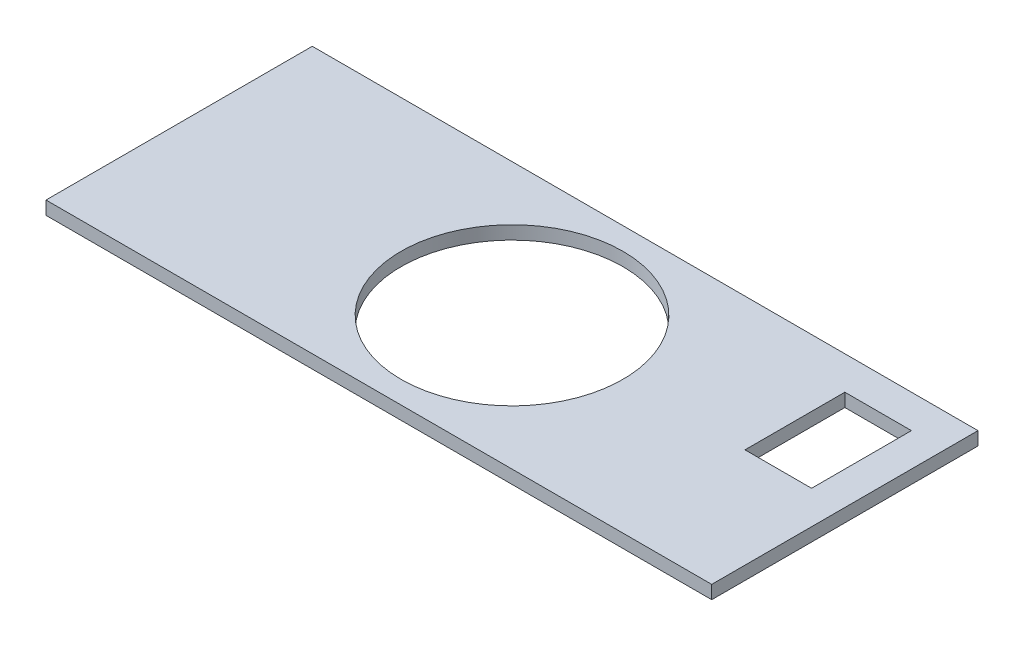
SolidWorks part; units mm, degrees
ref_plane "Front Plane" through (0, 0, 0) normal (0, 0, 1) x (1, 0, 0)
ref_plane "Top Plane" through (0, 0, 0) normal (0, 1, 0) x (1, 0, 0)
ref_plane "Right Plane" through (0, 0, 0) normal (1, 0, 0) x (0, 0, -1)
sketch "Sketch1" plane through (0, 0, 0) normal (0, 1, 0) x (1, 0, 0)
  line L0 (150, 120) -> (150, 60)
  line L1 (0, 0) -> (300, 0)
  line L2 (0, 0) -> (0, 120)
  line L3 (0, 120) -> (300, 120)
  line L4 (300, 0) -> (300, 120)
  line L6 (300, 120) -> (285, 120)
  line L7 (300, 120) -> (300, 60)
  line L11 (285, 60) -> (255, 60)
  line L12 (285, 60) -> (285, 105)
  line L13 (285, 105) -> (255, 105)
  line L14 (255, 60) -> (255, 105)
  circle A0 centre (150, 60) radius 50
  dimension "D4" = 100
  dimension "D1" = 300
  dimension "D2" = 120
  dimension "D3" = 60
  dimension "D5" = 15
  dimension "D7" = 30
extrude "Boss-Extrude1" add sketch "Sketch1" along normal blind 6
